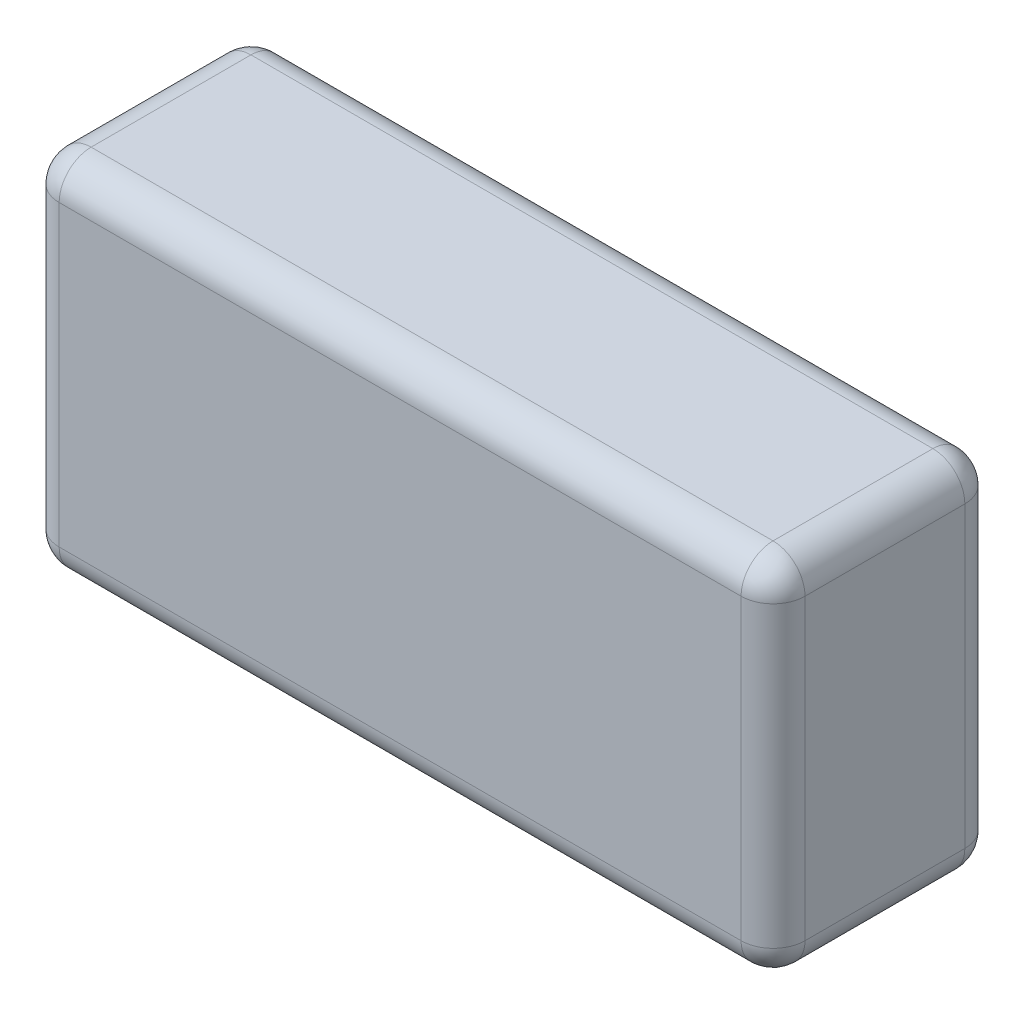
SolidWorks part; units mm, degrees
ref_plane "前视基准面" through (0, 0, 0) normal (0, 0, 1) x (1, 0, 0)
ref_plane "上视基准面" through (0, 0, 0) normal (0, 1, 0) x (1, 0, 0)
ref_plane "右视基准面" through (0, 0, 0) normal (1, 0, 0) x (0, 0, -1)
sketch "草图1" plane through (0, 0, 0) normal (0, 1, 0) x (1, 0, 0)
  line L1 (35, -10.5) -> (-35, -10.5)
  line L2 (35, -10.5) -> (35, 10.5)
  line L3 (35, 10.5) -> (-35, 10.5)
  line L4 (-35, -10.5) -> (-35, 10.5)
  line L5 (35, -10.5) -> (-35, 10.5) construction
  line L6 (35, 10.5) -> (-35, -10.5) construction
  point P0 (0, 0)
extrude "凸台-拉伸1" add sketch "草图1" along normal mid plane 34
fillet "圆角1" radius 3 12 edges at (-35, 0, -10.5) (0, -17, -10.5) (35, 0, -10.5) (35, -17, 0) (-35, 0, 10.5) (35, 0, 10.5) (0, -17, 10.5) (0, 17, -10.5) (35, 17, 0) (0, 17, 10.5) (-35, 17, 0) (-35, -17, 0)
